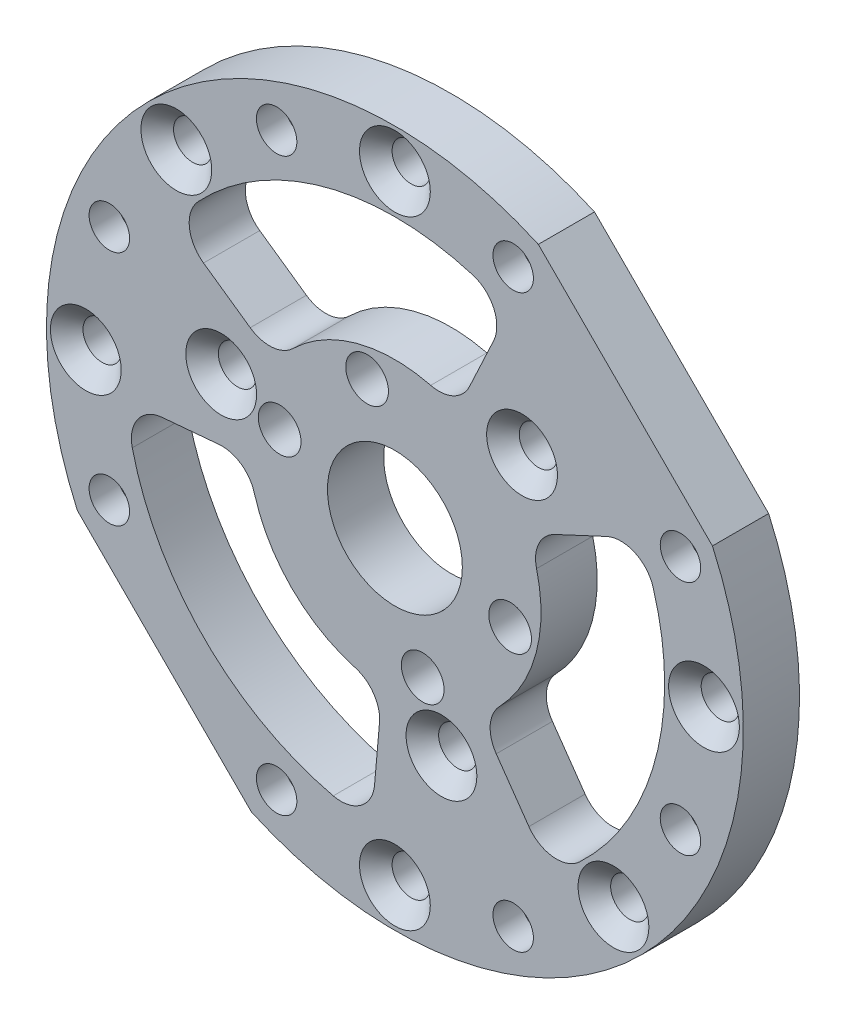
SolidWorks part; units mm, degrees
material "ABS"
ref_plane "正面" through (0, 0, 0) normal (0, 0, 1) x (1, 0, 0)
ref_plane "平面" through (0, 0, 0) normal (0, 1, 0) x (1, 0, 0)
ref_plane "右側面" through (0, 0, 0) normal (1, 0, 0) x (0, 0, -1)
sketch "ｽｹｯﾁ1" plane through (0, 0, 0) normal (0, 0, 1) x (1, 0, 0)
  circle A0 centre (0, 0) radius 31
  dimension "D1" = 62
extrude "ﾎﾞｽ - 押し出し1" add sketch "ｽｹｯﾁ1" along normal blind 5
sketch "ｽｹｯﾁ2" plane through (0, 0, 5) normal (0, 0, 1) x (1, 0, 0)
  circle A0 centre (0, 0) radius 6
  dimension "D1" = 12
extrude "ｶｯﾄ - 押し出し1" cut sketch "ｽｹｯﾁ2" against normal through all
sketch "ｽｹｯﾁ3" plane through (0, 0, 5) normal (0, 0, 1) x (1, 0, 0)
  circle A0 centre (0, 0) radius 27.5 construction
  circle A1 centre (0, 0) radius 31 construction
  dimension "D1" = 3.5
hole_wizard "M3 平皿頭ねじ用皿穴1" positions "ｽｹｯﾁ4" profile "ｽｹｯﾁ5" countersink size "M3" standard "JIS" end condition through all
sketch "ｽｹｯﾁ4" plane through (0, 0, 5) normal (0, 0, 1) x (1, 0, 0)
  circle A0 centre (0, 0) radius 27.5 construction
  point P0 (0, 27.5)
sketch "ｽｹｯﾁ5" plane through (0, 27.5, 5) normal (1, 0, 0) x (0, -1, 0)
  line L0 (0, 0) -> (0, 5)
  line L1 (0, 5) -> (1.7, 5)
  line L2 (1.7, 5) -> (1.7, 1.45)
  line L3 (1.7, 1.45) -> (3.15, 0)
  line L5 (3.15, 0) -> (0, 0)
  line L6 (-1.7, 1.45) -> (-3.15, 0) construction
  line L11 (0, -6.35) -> (0, 107.95) construction
  dimension "通し穴の直径" = 3.4
  dimension "通し穴の深さ" = 5
  dimension "表面の皿穴の直径" = 6.3
  dimension "表面の皿穴の角度" = 90
pattern_circular "円形ﾊﾟﾀｰﾝ1" count 8 over 360 about axis through (0, 0, 0) along (0, 0, 1) skipping 3, 7 of "M3 平皿頭ねじ用皿穴1"
sketch "ｽｹｯﾁ6" plane through (0, 0, 5) normal (0, 0, 1) x (1, 0, 0)
  line L1 (0, 41.0122) -> (41.0122, 0)
  line L2 (0, 41.0122) -> (-41.0122, 0)
  line L3 (-41.0122, 0) -> (0, -41.0122)
  line L4 (41.0122, 0) -> (0, -41.0122)
  line L5 (0, 41.0122) -> (0, -41.0122) construction
  line L6 (-41.0122, 0) -> (41.0122, 0) construction
  circle A0 centre (0, 0) radius 31 construction
  point P0 (0, 0)
  dimension "D1" = 29
extrude "ｶｯﾄ - 押し出し2" cut sketch "ｽｹｯﾁ6" against normal through all
hole_wizard "M3 平皿頭ねじ用皿穴2" [suppressed] positions "ｽｹｯﾁ8" profile "ｽｹｯﾁ9" countersink size "M3" standard "JIS"
sketch "ｽｹｯﾁ8" plane through (0, 0, 5) normal (0, 0, 1) x (1, 0, 0)
  line L0 (0, 9.5) -> (0, 0) construction
  point P0 (0, 9.5)
  dimension "D1" = 9.5
sketch "ｽｹｯﾁ9" plane through (0, 9.5, 5) normal (1, 0, 0) x (0, -1, 0)
  line L0 (0, 0) -> (0, 5)
  line L1 (0, 5) -> (1.8, 5)
  line L2 (1.8, 5) -> (1.8, 1.35)
  line L3 (1.8, 1.35) -> (3.15, 0)
  line L5 (3.15, 0) -> (0, 0)
  line L6 (-1.8, 1.35) -> (-3.15, 0) construction
  line L11 (0, -6.35) -> (0, 107.95) construction
  dimension "通し穴の直径" = 3.6
  dimension "通し穴の深さ" = 5
  dimension "表面の皿穴の直径" = 6.3
  dimension "表面の皿穴の角度" = 90
pattern_circular "円形ﾊﾟﾀｰﾝ2" [suppressed] count 4 over 360
hole_wizard "M3 平皿頭ねじ用皿穴4" positions "ｽｹｯﾁ10" profile "ｽｹｯﾁ12" countersink size "M3" standard "JIS" end condition through all
sketch "ｽｹｯﾁ10" plane through (0, 0, 5) normal (0, 0, 1) x (1, 0, 0)
  line L2 (20.5061, 20.5061) -> (0, 0) construction
  line L3 (12.7601, 28.2521) -> (28.2521, 12.7601) construction
  point P0 (11.3137, 11.3137)
  point P24 (20.5061, 20.5061)
  dimension "D1" = 16
sketch "ｽｹｯﾁ12" plane through (11.3137, 11.3137, 5) normal (1, 0, 0) x (0, -1, 0)
  line L0 (0, 0) -> (0, 5)
  line L1 (0, 5) -> (1.7, 5)
  line L2 (1.7, 5) -> (1.7, 1.45)
  line L3 (1.7, 1.45) -> (3.15, 0)
  line L5 (3.15, 0) -> (0, 0)
  line L6 (-1.7, 1.45) -> (-3.15, 0) construction
  line L11 (0, -6.35) -> (0, 107.95) construction
  dimension "通し穴の直径" = 3.4
  dimension "通し穴の深さ" = 5
  dimension "表面の皿穴の直径" = 6.3
  dimension "表面の皿穴の角度" = 90
pattern_circular "円形ﾊﾟﾀｰﾝ3" count 3 over 360 about axis through (0, 0, 0) along (0, 0, 1) of "M3 平皿頭ねじ用皿穴4"
sketch "ｽｹｯﾁ14" [suppressed] plane through (0, 0, 5) normal (0, 0, 1) x (1, 0, 0)
  line L0 (0, 0) -> (19.4454, -19.4454) construction
  line L2 (4.2525, -8.4951) -> (5.4639, -22.3416)
  line L3 (8.4951, -4.2525) -> (22.3416, -5.4639)
  circle A0 centre (0, 0) radius 9.5 construction
  circle A1 centre (0, 0) radius 23 construction
  arc A2 (4.2525, -8.4951) -> (8.4951, -4.2525) centre (0, 0) ccw
  arc A3 (5.4639, -22.3416) -> (22.3416, -5.4639) centre (0, 0) ccw
  dimension "D1" = 46
  dimension "D2" = 40
  dimension "D3" = 6
extrude "ｶｯﾄ - 押し出し3" [suppressed] cut sketch "ｽｹｯﾁ14" against normal through all
fillet "ﾌｨﾚｯﾄ1" [suppressed] radius 1
pattern_circular "円形ﾊﾟﾀｰﾝ4" [suppressed] count 4 over 360
sketch "ｽｹｯﾁ15" plane through (0, 0, 0) normal (0, 0, 1) x (1, 0, 0)
  line L1 (0, 15.7668) -> (2.8, 17.3834)
  line L2 (2.8, 17.3834) -> (2.8, 20.6166)
  line L3 (2.8, 20.6166) -> (0, 22.2332)
  line L4 (0, 22.2332) -> (-2.8, 20.6166)
  line L5 (-2.8, 20.6166) -> (-2.8, 17.3834)
  line L6 (-2.8, 17.3834) -> (0, 15.7668)
  circle A0 centre (0, 0) radius 19 construction
  circle A2 centre (0, 19) radius 2.8 construction
  dimension "D1" = 38
  dimension "D2" = 5.6
sketch "ｽｹｯﾁ16" plane through (0, 0, 0) normal (0, 0, -1) x (-1, 0, 0)
  line L0 (10.5238, 25.4067) -> (0, 0) construction
  line L1 (10.942, 22.2298) -> (13.4842, 24.1805)
  line L2 (13.4842, 24.1805) -> (13.0659, 27.3573)
  line L3 (13.0659, 27.3573) -> (10.1056, 28.5836)
  line L4 (10.1056, 28.5836) -> (7.5634, 26.6329)
  line L5 (7.5634, 26.6329) -> (7.9817, 23.456)
  line L6 (7.9817, 23.456) -> (10.942, 22.2298)
  arc A0 (0, 27.5) -> (19.4454, 19.4454) centre (0, 0) cw construction
  circle A1 centre (10.5238, 25.4067) radius 2.775 construction
  point P3 (0, 0)
  point P8 (0, 0)
  dimension "D1" = 5.55
extrude "ｶｯﾄ - 押し出し5" cut sketch "ｽｹｯﾁ16" against normal blind 2.5
hole_wizard "M3 すきま穴2" positions "ｽｹｯﾁ18" profile "ｽｹｯﾁ19" hole size "M3" standard "JIS" end condition through all
sketch "ｽｹｯﾁ18" plane through (0, 0, 2.5) normal (0, 0, -1) x (-1, 0, 0)
  point P0 (10.5238, 25.4067)
sketch "ｽｹｯﾁ19" plane through (-10.5238, 25.4067, 2.5) normal (1, 0, 0) x (0, 1, 0)
  line L0 (0, 0) -> (0, 2.5)
  line L1 (0, 2.5) -> (1.8, 2.5)
  line L2 (1.8, 2.5) -> (1.8, 0)
  line L5 (1.8, 0) -> (0, 0)
  line L11 (0, -6.35) -> (0, 107.95) construction
  dimension "通し穴の直径" = 3.6
  dimension "通し穴の深さ" = 2.5
sketch "ｽｹｯﾁ17" plane through (0, 0, 0) normal (0, 0, -1) x (-1, 0, 0)
  circle A0 centre (10.1056, 28.5836) radius 0.3
  dimension "D1" = 0.6
extrude "ｶｯﾄ - 押し出し6" cut sketch "ｽｹｯﾁ17" against normal blind 2.5
pattern_circular "円形ﾊﾟﾀｰﾝ6" count 6 over 360 about axis through (-10.5238, 25.4067, 0) along (0, 0, 1) of "ｶｯﾄ - 押し出し6"
pattern_circular "円形ﾊﾟﾀｰﾝ7" count 8 over 360 about axis through (0, 0, 0) along (0, 0, 1) of "ｶｯﾄ - 押し出し5", "M3 すきま穴2", "円形ﾊﾟﾀｰﾝ6", "ｶｯﾄ - 押し出し6"
extrude "ｶｯﾄ - 押し出し7" [suppressed] cut sketch "ｽｹｯﾁ15" along normal blind 2.5
hole_wizard "M3 すきま穴3" [suppressed] positions "ｽｹｯﾁ22" profile "ｽｹｯﾁ21" hole size "M3" standard "JIS"
sketch "ｽｹｯﾁ22" [suppressed] plane through (0, 0, 2.5) normal (0, 0, -1) x (-1, 0, 0)
  point P0 (0, 19)
sketch "ｽｹｯﾁ21" plane through (0, 19, 2.5) normal (1, 0, 0) x (0, 1, 0)
  line L0 (0, 0) -> (0, 2.5)
  line L1 (0, 2.5) -> (1.8, 2.5)
  line L2 (1.8, 2.5) -> (1.8, 0)
  line L5 (1.8, 0) -> (0, 0)
  line L11 (0, -6.35) -> (0, 107.95) construction
  dimension "通し穴の直径" = 3.6
  dimension "通し穴の深さ" = 2.5
sketch "ｽｹｯﾁ23" [suppressed] plane through (0, 0, 0) normal (0, 0, -1) x (-1, 0, 0)
  circle A0 centre (0, 22.2332) radius 0.4
  dimension "D1" = 0.8
extrude "ｶｯﾄ - 押し出し8" [suppressed] cut sketch "ｽｹｯﾁ23" against normal up to surface (2.5 mm away)
pattern_circular "円形ﾊﾟﾀｰﾝ8" [suppressed] count 6 over 360
pattern_circular "円形ﾊﾟﾀｰﾝ9" [suppressed] count 4 over 360
sketch "ｽｹｯﾁ24" plane through (0, 0, 5) normal (0, 0, 1) x (1, 0, 0)
  line L0 (20.5061, 20.5061) -> (0, 0) construction
  line L1 (12.7601, 28.2521) -> (28.2521, 12.7601) construction
  line L2 (0, 0) -> (4.1411, -15.4548) construction
  line L3 (4.1411, -15.4548) -> (8.0234, -29.9437) construction
  line L4 (7.4565, -10.649) -> (13.7658, -19.6596)
  line L5 (21.7514, 10.1428) -> (11.782, 5.494)
  line L6 (23.1822, -6.2117) -> (12.557, -3.3646) construction
  line L7 (12.557, -3.3646) -> (0, 0) construction
  line L8 (11.782, 5.494) -> (0, 0) construction
  line L9 (0, 0) -> (7.4565, -10.649) construction
  circle A0 centre (0, 0) radius 10 construction
  circle A1 centre (0, 0) radius 24 construction
  arc A3 (-12.7601, -28.2521) -> (28.2521, 12.7601) centre (0, 0) ccw construction
  arc A4 (11.782, 5.494) -> (7.4565, -10.649) centre (0, 0) cw
  arc A5 (21.7514, 10.1428) -> (13.7658, -19.6596) centre (0, 0) cw
  dimension "D1" = 48
  dimension "D2" = 20
  dimension "D5" = 13
  dimension "D3" = 80
  dimension "D4" = 60
extrude "ｶｯﾄ - 押し出し9" cut sketch "ｽｹｯﾁ24" against normal through all
fillet "ﾌｨﾚｯﾄ2" radius 3 4 edges at (13.7658, -19.6596, 2.5) (21.7514, 10.1428, 2.5) (7.4565, -10.649, 2.5) (11.782, 5.494, 2.5)
pattern_circular "円形ﾊﾟﾀｰﾝ10" count 3 over 360 about axis through (0, 0, 0) along (0, 0, 1) of "ﾌｨﾚｯﾄ2", "ｶｯﾄ - 押し出し9"
sketch "ｽｹｯﾁ25" plane through (0, 0, 5) normal (0, 0, 1) x (1, 0, 0)
  line L1 (2.4749, -10.253) -> (-10.253, 2.4749)
  line L2 (2.4749, -10.253) -> (10.253, -2.4749)
  line L3 (10.253, -2.4749) -> (-2.4749, 10.253)
  line L4 (-10.253, 2.4749) -> (-2.4749, 10.253)
  line L5 (2.4749, -10.253) -> (-2.4749, 10.253) construction
  line L6 (10.253, -2.4749) -> (-10.253, 2.4749) construction
  line L8 (12.7601, 28.2521) -> (28.2521, 12.7601) construction
  point P0 (0, 0)
  dimension "D1" = 11
  dimension "D2" = 18
sketch "ｽｹｯﾁ26" plane through (0, 0, 5) normal (0, 0, 1) x (1, 0, 0)
  circle A0 centre (-2.4749, 10.253) radius 1.9
  circle A1 centre (10.253, -2.4749) radius 1.9
  circle A2 centre (-10.253, 2.4749) radius 1.9
  circle A3 centre (2.4749, -10.253) radius 1.9
  dimension "D1" = 3.8
extrude "ｶｯﾄ - 押し出し10" cut sketch "ｽｹｯﾁ26" against normal blind 3.5
